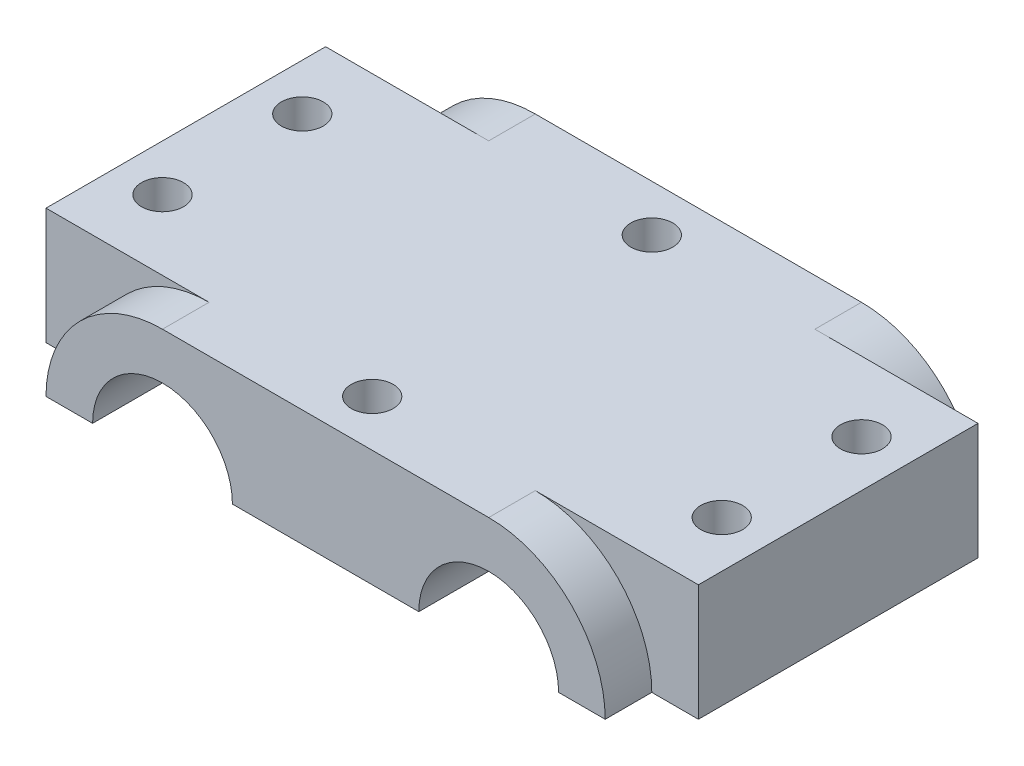
SolidWorks part; units mm, degrees
ref_plane "Front Plane" through (0, 0, 0) normal (0, 0, 1) x (1, 0, 0)
ref_plane "Top Plane" through (0, 0, 0) normal (0, 1, 0) x (1, 0, 0)
ref_plane "Right Plane" through (0, 0, 0) normal (1, 0, 0) x (0, 0, -1)
sketch "Sketch1" plane through (0, 0, 0) normal (0, 0, 1) x (1, 0, 0)
  line L0 (35, 33.111) -> (35, -7.6597) construction
  line L1 (0, 0) -> (10, 0)
  line L2 (0, 0) -> (0, 12.5)
  line L3 (0, 12.5) -> (70, 12.5)
  line L4 (70, 0) -> (70, 12.5)
  line L5 (60, 0) -> (70, 0)
  line L6 (25, 0) -> (45, 0)
  arc A0 (25, 0) -> (10, 0) centre (17.5, 0) ccw
  arc A1 (60, 0) -> (45, 0) centre (52.5, 0) ccw
  point P11 (0, 0)
  dimension "D3" = 15
  dimension "D1" = 12.5
  dimension "D2" = 70
  dimension "D4" = 35
extrude "Boss-Extrude1" add sketch "Sketch1" along normal blind 40
sketch "Sketch2" plane through (0, 0, 40) normal (0, 0, 1) x (1, 0, 0)
  line L0 (35, 27.9645) -> (35, -12.8288) construction
  line L1 (0, 12.5) -> (0, 0) construction
  line L2 (70, 0) -> (70, 12.5) construction
  line L3 (0, 0) -> (10, 0) construction
  line L4 (60, 0) -> (70, 0) construction
  line L5 (70, 12.5) -> (0, 12.5) construction
  line L6 (0, 0) -> (5, 0)
  line L7 (0, 12.5) -> (0, 0)
  line L8 (65, 0) -> (70, 0)
  line L9 (70, 0) -> (70, 12.5)
  line L10 (70, 12.5) -> (52.5, 12.5)
  line L11 (17.5, 12.5) -> (0, 12.5)
  arc A0 (65, 0) -> (52.5, 12.5) centre (52.5, 0) ccw
  arc A1 (5, 0) -> (17.5, 12.5) centre (17.5, 0) cw
  dimension "D1" = 25
extrude "Cut-Extrude1" cut sketch "Sketch2" against normal blind 5
ref_plane "Plane1" through (0, 0, 20) normal (0, 0, -1) x (-1, 0, 0)
mirror "Mirror1" about plane through (0, 0, 20) normal (0, 0, -1) of "Cut-Extrude1"
sketch "Sketch3" plane through (0, 12.5, 0) normal (0, 1, 0) x (1, 0, 0)
  line L0 (52.5, 0) -> (17.5, 0) construction
  line L2 (65, -5) -> (52.5, -5) construction
  line L3 (17.5, -5) -> (0, -5) construction
  line L4 (0, -35) -> (0, -5) construction
  line L5 (70, -5) -> (52.5, -5) construction
  line L6 (70, -35) -> (70, -5) construction
  line L7 (17.5, -35) -> (0, -35) construction
  line L8 (70, -35) -> (52.5, -35) construction
  circle A0 centre (35, -5) radius 2.25
  circle A1 centre (35, -35) radius 2.25
  circle A2 centre (5, -12.5) radius 2.25
  circle A3 centre (5, -27.5) radius 2.25
  circle A4 centre (65, -12.5) radius 2.25
  circle A5 centre (65, -27.5) radius 2.25
  point P12 (0, 0)
  point P15 (35, 0)
  point P18 (0, 0)
  point P19 (0, 0)
  point P28 (0, 0)
  point P29 (0, 0)
  point P32 (0, 0)
  point P33 (0, 0)
  point P36 (0, 0)
  dimension "D1" = 4.5
  dimension "D2" = 7.5
  dimension "D3" = 5
  dimension "D4" = 7.5
  dimension "D5" = 5
  dimension "D6" = 7.5
extrude "Cut-Extrude2" cut sketch "Sketch3" against normal up to next
